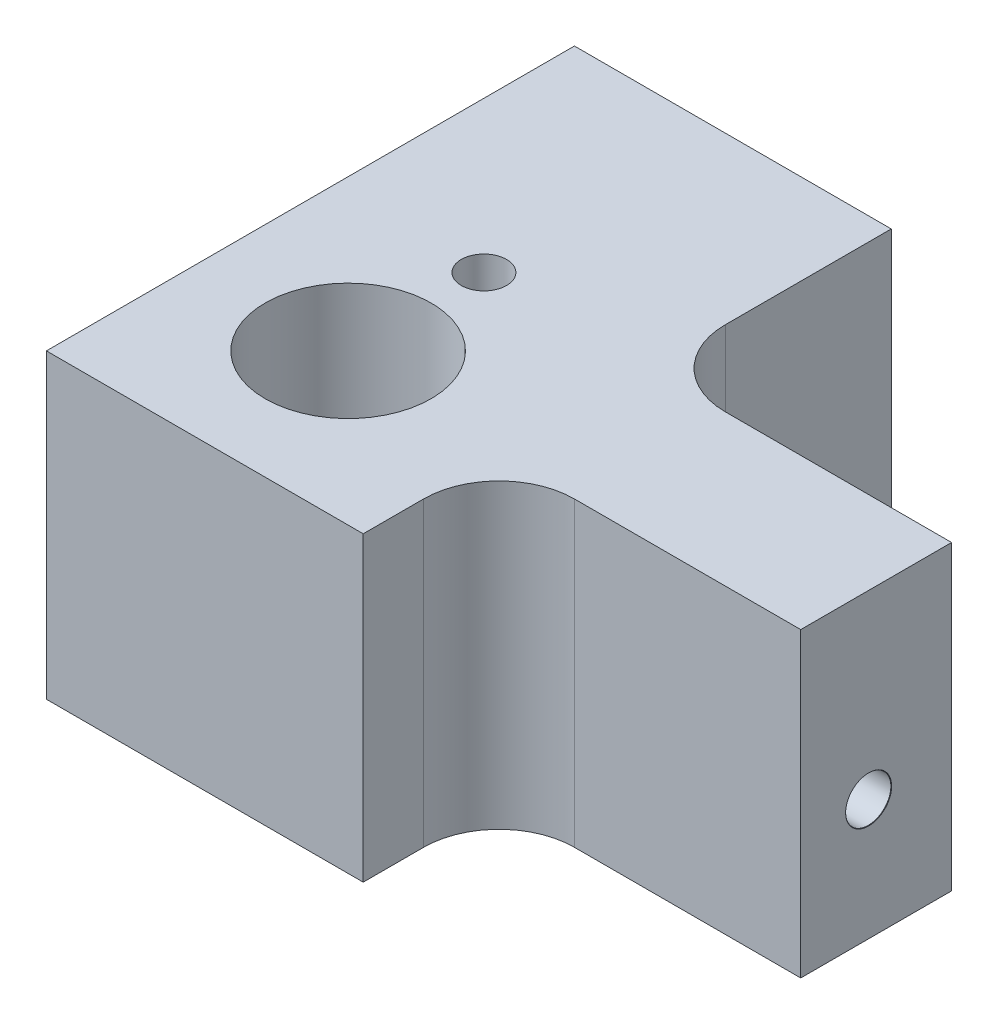
SolidWorks part; units mm, degrees
ref_plane "Front Plane" through (0, 0, 0) normal (0, 0, 1) x (1, 0, 0)
ref_plane "Top Plane" through (0, 0, 0) normal (0, 1, 0) x (1, 0, 0)
ref_plane "Right Plane" through (0, 0, 0) normal (1, 0, 0) x (0, 0, -1)
sketch "Sketch1" plane through (0, 0, 0) normal (0, 1, 0) x (1, 0, 0)
  line L1 (-10.5256, 22.3096) -> (38.4744, 22.3096)
  line L2 (-10.5256, 22.3096) -> (-10.5256, -12.6904)
  line L3 (-10.5256, -12.6904) -> (38.4744, -12.6904)
  line L4 (38.4744, 22.3096) -> (38.4744, -12.6904)
  dimension "D1" = 35
  dimension "D2" = 49
extrude "Boss-Extrude1" add sketch "Sketch1" along normal blind 20
hole_wizard "Ø3.0mm Dowel Hole1" positions "Sketch3" profile "Sketch4" hole size "Ø3.0" standard "ANSI Metric"
sketch "Sketch3" plane through (0, 0, -22.3096) normal (0, 0, -1) x (-1, 0, 0)
  line L0 (-38.4744, 20) -> (-38.4744, 0) construction
  line L3 (-38.4744, 0) -> (10.5256, 0) construction
  point P0 (-7.4744, 4)
  dimension "D1" = 31
  dimension "D2" = 4
sketch "Sketch4" plane through (7.4744, 4, -22.3096) normal (1, 0, 0) x (0, 1, 0)
  line L0 (0, 0) -> (0, 12)
  line L1 (0, 12) -> (1.5, 11.0987)
  line L2 (1.5, 11.0987) -> (1.5, 0.025)
  line L3 (1.5, 0.025) -> (1.525, 0)
  line L5 (1.525, 0) -> (0, 0)
  line L6 (-1.5, 0.025) -> (-1.525, 0) construction
  line L10 (0, 12) -> (-1.5, 11.0987) construction
  line L11 (0, -6.35) -> (0, 107.95) construction
  dimension "Hole Dia." = 3
  dimension "Hole Depth" = 12
  dimension "Near C'Sink Dia." = 3.05
  dimension "Near C'Sink Angle" = 90
  dimension "Drill Angle" = 118
hole_wizard "Ø3.0mm Dowel Hole2" positions "Sketch7" profile "Sketch8" hole size "Ø3.0" standard "ANSI Metric"
sketch "Sketch7" plane through (38.4744, 0, 0) normal (1, 0, 0) x (0, 0, -1)
  line L0 (-12.6904, 0) -> (22.3096, 0) construction
  line L1 (22.3096, 20) -> (22.3096, 0) construction
  point P0 (0.8096, 8)
  dimension "D1" = 8
  dimension "D2" = 21.5
sketch "Sketch8" plane through (38.4744, 8, -0.8096) normal (0, 1, 0) x (0, 0, -1)
  line L0 (0, 0) -> (0, 12.9013)
  line L1 (0, 12.9013) -> (1.5, 12)
  line L2 (1.5, 12) -> (1.5, 0.025)
  line L3 (1.5, 0.025) -> (1.525, 0)
  line L5 (1.525, 0) -> (0, 0)
  line L6 (-1.5, 0.025) -> (-1.525, 0) construction
  line L10 (0, 12.9013) -> (-1.5, 12) construction
  line L11 (0, -6.35) -> (0, 107.95) construction
  dimension "Hole Dia." = 3
  dimension "Hole Depth" = 12
  dimension "Near C'Sink Dia." = 3.05
  dimension "Near C'Sink Angle" = 90
  dimension "Drill Angle" = 118
hole_wizard "Ø3.0mm Dowel Hole3" positions "Sketch9" profile "Sketch10" hole size "Ø3.0" standard "ANSI Metric" end condition through all
sketch "Sketch9" plane through (0, 0, 0) normal (0, -1, 0) x (-1, 0, 0)
  line L1 (-38.4744, 22.3096) -> (10.5256, 22.3096) construction
  line L3 (-38.4744, -12.6904) -> (-38.4744, 22.3096) construction
  point P0 (-7.4744, 6.3096)
  dimension "D1" = 31
  dimension "D2" = 16
sketch "Sketch10" plane through (7.4744, 0, -6.3096) normal (1, 0, 0) x (0, 0, -1)
  line L0 (0, 0) -> (0, 20)
  line L1 (0, 20) -> (1.5, 20)
  line L2 (1.5, 20) -> (1.5, 0.025)
  line L3 (1.5, 0.025) -> (1.525, 0)
  line L5 (1.525, 0) -> (0, 0)
  line L6 (-1.5, 0.025) -> (-1.525, 0) construction
  line L11 (0, -6.35) -> (0, 107.95) construction
  dimension "Thru Hole Dia." = 3
  dimension "Thru Hole Depth" = 20
  dimension "Near C'Sink Dia." = 3.05
  dimension "Near C'Sink Angle" = 90
sketch "Sketch14" plane through (0, 20, 0) normal (0, 1, 0) x (1, 0, 0)
  line L0 (-10.5256, -12.6904) -> (38.4744, -12.6904) construction
  line L1 (-10.5256, 22.3096) -> (-2.5256, 22.3096)
  line L2 (-10.5256, 22.3096) -> (-10.5256, -12.6904)
  line L3 (-10.5256, -12.6904) -> (-2.5256, -12.6904)
  line L4 (-2.5256, 22.3096) -> (-2.5256, -12.6904)
  line L7 (18.4744, 22.3096) -> (38.4744, 22.3096)
  line L8 (18.4744, 22.3096) -> (18.4744, 6.3096)
  line L9 (18.4744, 6.3096) -> (38.4744, 6.3096)
  line L10 (38.4744, 22.3096) -> (38.4744, 6.3096)
  line L13 (38.4744, -12.6904) -> (18.4744, -12.6904)
  line L14 (38.4744, -12.6904) -> (38.4744, -3.6904)
  line L15 (38.4744, -3.6904) -> (18.4744, -3.6904)
  line L16 (18.4744, -12.6904) -> (18.4744, -3.6904)
  dimension "D1" = 0
  dimension "D2" = 8
  dimension "D3" = 9
  dimension "D4" = 20
  dimension "D5" = 10
  dimension "D6" = 20
extrude "Cut-Extrude3" cut sketch "Sketch14" against normal blind 28
sketch "Sketch15" plane through (0, 20, 0) normal (0, 1, 0) x (1, 0, 0)
  line L0 (18.4744, 22.3096) -> (-2.5256, 22.3096) construction
  circle A0 centre (7.4744, -2.6904) radius 5.5
  dimension "D1" = 25
  dimension "D2" = 11
extrude "Cut-Extrude4" cut sketch "Sketch15" against normal blind 30
fillet "Fillet1" radius 5 2 edges at (18.4744, 10, 3.6904) (18.4744, 10, -6.3096)
